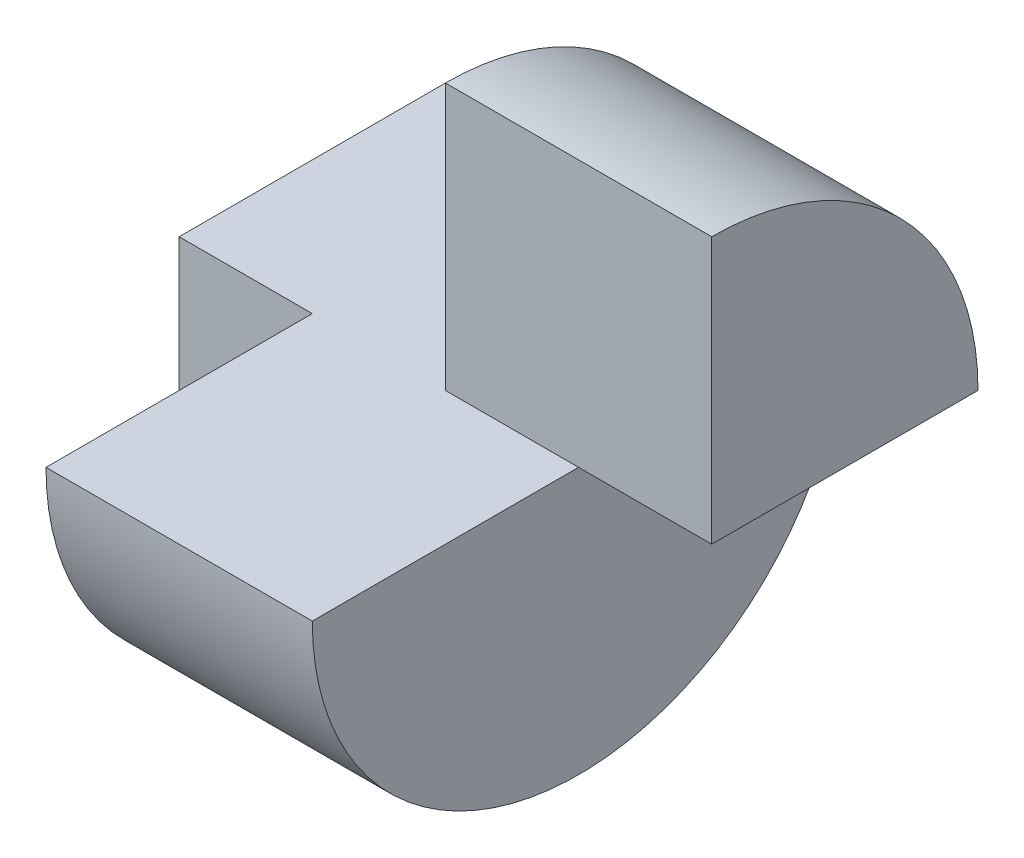
SolidWorks part; units mm, degrees
ref_plane "Front Plane" through (0, 0, 0) normal (0, 0, 1) x (1, 0, 0)
ref_plane "Top Plane" through (0, 0, 0) normal (0, 1, 0) x (1, 0, 0)
ref_plane "Right Plane" through (0, 0, 0) normal (1, 0, 0) x (0, 0, -1)
sketch "Sketch1" plane through (0, 0, 0) normal (0, 0, 1) x (1, 0, 0)
  line L1 (0, 0) -> (40, 0)
  line L2 (0, 0) -> (0, 40)
  line L3 (0, 40) -> (40, 40)
  line L4 (40, 0) -> (40, 40)
  dimension "D1" = 40
  dimension "D2" = 40
extrude "Boss-Extrude1" add sketch "Sketch1" along normal blind 40
sketch "Sketch2" plane through (0, 0, 40) normal (0, 0, 1) x (1, 0, 0)
  line L1 (0, 40) -> (20, 40)
  line L2 (0, 40) -> (0, 20)
  line L3 (0, 20) -> (20, 20)
  line L4 (20, 40) -> (20, 20)
  line L5 (40, 0) -> (30, 0)
  line L6 (40, 0) -> (40, 20)
  line L7 (40, 20) -> (30, 20)
  line L8 (30, 0) -> (30, 20)
  dimension "D1" = 20
  dimension "D2" = 20
  dimension "D3" = 20
  dimension "D4" = 10
extrude "Cut-Extrude1" cut sketch "Sketch2" against normal blind 40
sketch "Sketch3" plane through (20, 0, 0) normal (-1, 0, 0) x (0, 0, 1)
  line L0 (0, 20) -> (40, 20) construction
  line L1 (40, 40) -> (20, 40)
  line L2 (40, 40) -> (40, 20)
  line L3 (40, 20) -> (20, 20)
  line L4 (20, 40) -> (20, 20)
  dimension "D1" = 20
extrude "Cut-Extrude2" cut sketch "Sketch3" against normal blind 40
sketch "Sketch4" plane through (20, 0, 0) normal (-1, 0, 0) x (0, 0, 1)
  line L0 (0, 40) -> (20, 40) construction
  line L1 (20, 40) -> (0, 40)
  line L2 (0, 40) -> (0, 20)
  arc A0 (0, 20) -> (20, 40) centre (20, 20) cw
extrude "Cut-Extrude3" cut sketch "Sketch4" against normal blind 40
sketch "Sketch5" plane through (0, 0, 0) normal (-1, 0, 0) x (0, 0, 1)
  line L0 (0, 20) -> (40, 20) construction
  line L1 (40, 0) -> (0, 0) construction
  line L2 (40, 20) -> (40, 0)
  line L3 (40, 0) -> (0, 0)
  line L4 (0, 0) -> (0, 20)
  arc A0 (40, 20) -> (20, 0) centre (20, 20) cw
  arc A1 (20, 0) -> (0, 20) centre (20, 20) cw
  line M1 (40, 0) -> (40, 20)
  line M3 (0, 20) -> (0, 0)
  line M4 (0, 0) -> (40, 0)
extrude "Cut-Extrude4" cut sketch "Sketch5" against normal blind 40 contours A1 M4 M3 | A0 L3 M1
sketch "Sketch6" plane through (0, 0, 0) normal (-1, 0, 0) x (0, 0, 1)
  line L0 (0, 20) -> (40, 20) construction
  line L1 (20, 0) -> (20, 20)
  line L2 (20, 20) -> (40, 20)
  arc A0 (40, 20) -> (20, 0) centre (20, 20) cw
extrude "Cut-Extrude5" cut sketch "Sketch6" against normal blind 10
